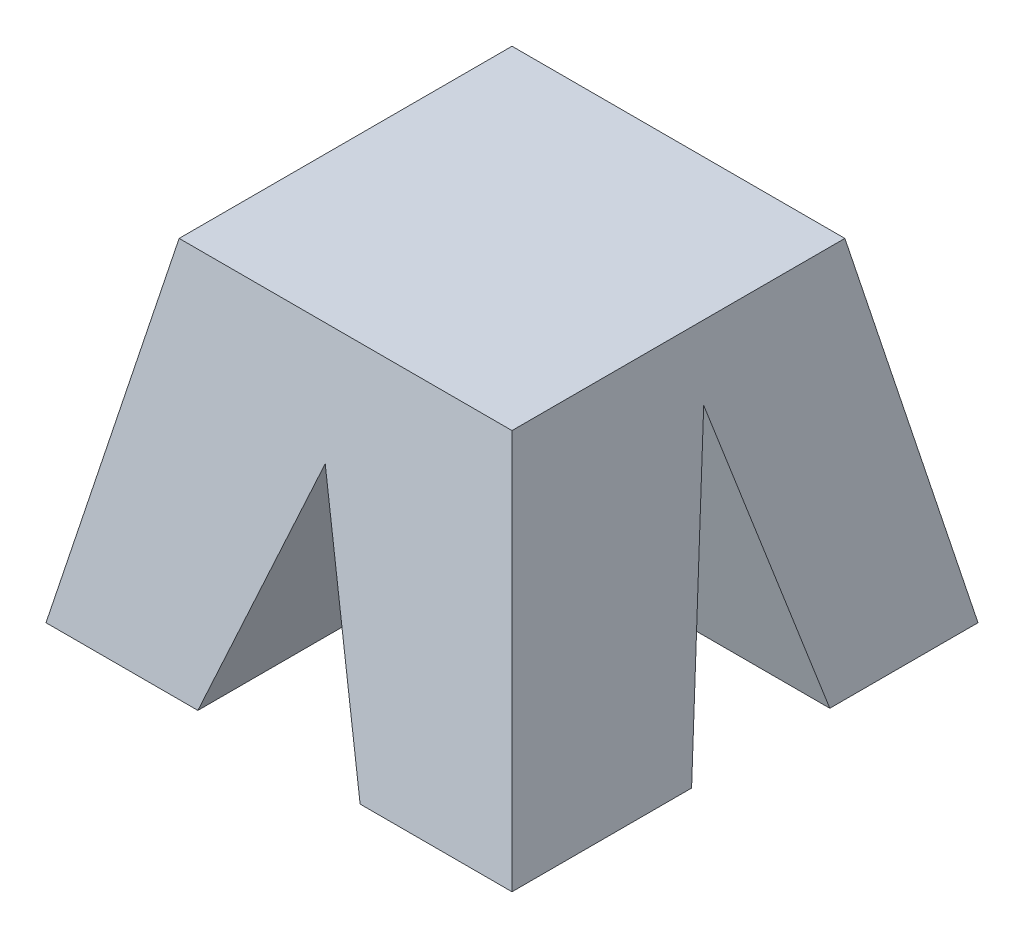
SolidWorks part; units mm, degrees
ref_plane "Front Plane" through (0, 0, 0) normal (0, 0, 1) x (1, 0, 0)
ref_plane "Top Plane" through (0, 0, 0) normal (0, 1, 0) x (1, 0, 0)
ref_plane "Right Plane" through (0, 0, 0) normal (1, 0, 0) x (0, 0, -1)
ref_plane "Plane4" through (0, -3, 0) normal (0, 1, 0) x (1, 0, 0)
ref_plane "Plane5" through (0, -5, 0) normal (0, 1, 0) x (1, 0, 0)
sketch "Sketch2" plane through (0, -3, 0) normal (0, -1, 0) x (1, 0, 0)
  line L1 (-1, 2) -> (1, 2)
  line L2 (-1, 2) -> (-1, 0)
  line L3 (-1, 0) -> (1, 0)
  line L4 (1, 2) -> (1, 0)
  dimension "D1" = 2
  dimension "D2" = 2
  dimension "D3" = 1
sketch "Sketch3" plane through (0, -5, 0) normal (0, -1, 0) x (-1, 0, 0)
  line L1 (-1.4, 0.4) -> (1.4, 0.4)
  line L2 (-1.4, 0.4) -> (-1.4, -2.4)
  line L3 (-1.4, -2.4) -> (1.4, -2.4)
  line L4 (1.4, 0.4) -> (1.4, -2.4)
  dimension "D1" = 2.8
  dimension "D2" = 2.8
  dimension "D3" = 1.4
  dimension "D4" = 0.4
loft "Loft1" add profiles "Sketch2", "Sketch3"
ref_plane "Plane2" through (0, 0, 3) normal (0, 0, 1) x (1, 0, 0)
sketch "Sketch4" plane through (0, 0, 3) normal (0, 0, 1) x (1, 0, 0)
  line L0 (0, -3.6115) -> (-0.5, -5.0359)
  line L2 (-0.5, -5.0359) -> (0.5, -5.0359)
  line L3 (0.5, -5.0359) -> (0, -3.6115)
  dimension "D1" = 0.5
  dimension "D2" = 0.5
  dimension "D3" = 3.6115
ref_plane "Plane3" through (1.8, 0, 0) normal (1, 0, 0) x (0, 0, -1)
sketch "Sketch7" plane through (1.8, 0, 0) normal (1, 0, 0) x (0, 0, -1)
  line L0 (-0.3952, -5.3589) -> (-0.9223, -3.3705)
  line L1 (-0.9223, -3.3705) -> (-1.444, -5.503)
  line L2 (-1.444, -5.503) -> (-0.3952, -5.3589)
extrude "Cut-Extrude1" cut sketch "Sketch7" against normal up to vertex
extrude "Cut-Extrude2" cut sketch "Sketch4" against normal up to vertex
equation "\"D3@Sketch3\"=\"D1@Sketch3\"/2"
equation "\"D4@Sketch3\"=(\"D2@Sketch3\"-2)/2"
